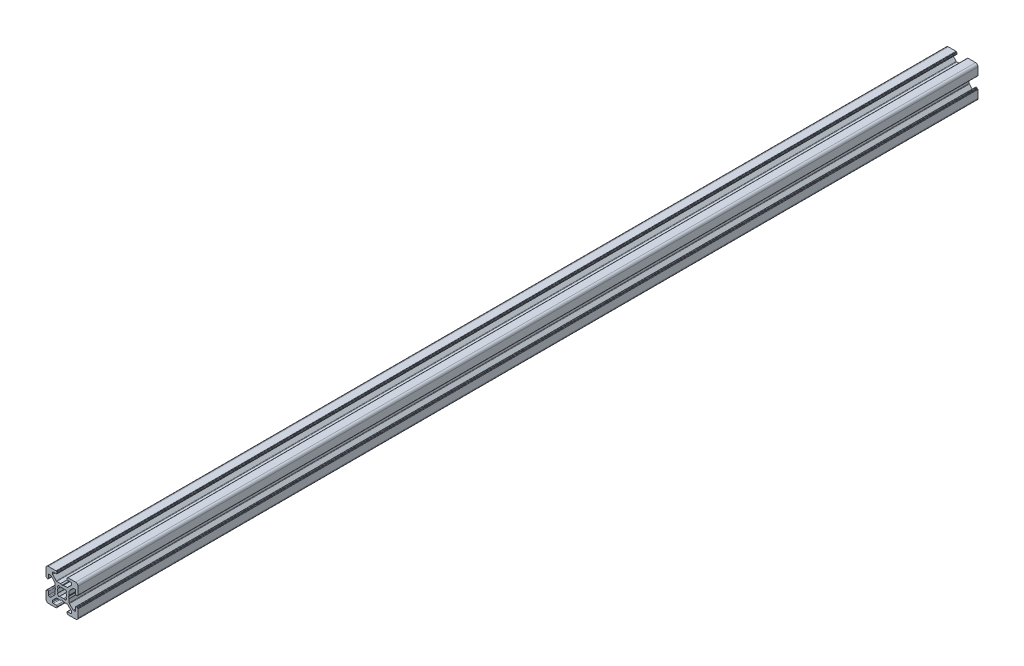
SolidWorks part; units mm, degrees
ref_plane "Front Plane" through (0, 0, 0) normal (0, 0, 1) x (1, 0, 0)
ref_plane "Top Plane" through (0, 0, 0) normal (0, 1, 0) x (1, 0, 0)
ref_plane "Right Plane" through (0, 0, 0) normal (1, 0, 0) x (0, 0, -1)
sketch "Sketch1" plane through (0, 0, 0) normal (0, 0, 1) x (1, 0, 0)
  line L0 (0, 13.3675) -> (0, -10.9159) construction
  line L1 (-12.9725, 0) -> (15.1887, 0) construction
  line L2 (-3.5, 8.5) -> (-5.5, 8.5)
  line L3 (-3.55, 9.7) -> (-3.55, 9.8)
  line L4 (-6, 7.2678) -> (-6, 8)
  line L5 (-7.2678, 6) -> (-8, 6)
  line L6 (-3.75, 10) -> (-8.5, 10)
  line L7 (-9.7, 3.55) -> (-9.8, 3.55)
  line L8 (-9.5, 3.2) -> (-9.5, 3.35)
  line L9 (-9, 3) -> (-9.3, 3)
  line L10 (-4.4732, 0.8536) -> (-4.0381, 0.1)
  line L11 (-4.5, 3.2322) -> (-4.5, 0.9536)
  line L12 (-8.5, 3.5) -> (-8.5, 5.5)
  line L13 (-10, 3.75) -> (-10, 8.5)
  line L14 (-3.5858, 4.6464) -> (-5.8536, 6.9142)
  line L15 (-4.6464, 3.5858) -> (-6.9142, 5.8536)
  line L16 (-3.2, 9.5) -> (-3.35, 9.5)
  line L17 (-3, 9) -> (-3, 9.3)
  line L18 (-0.8536, 4.4732) -> (-0.1, 4.0381)
  line L19 (-3.2322, 4.5) -> (-0.9536, 4.5)
  line L20 (-1.2582, 2.4453) -> (-1.9139, 2.9896)
  line L21 (-2.4453, 1.2582) -> (-2.9922, 1.9099)
  line L22 (3.5, -8.5) -> (5.5, -8.5)
  line L23 (3.55, -9.7) -> (3.55, -9.8)
  line L24 (6, -7.2678) -> (6, -8)
  line L25 (7.2678, -6) -> (8, -6)
  line L26 (3.75, -10) -> (8.5, -10)
  line L27 (9.7, -3.55) -> (9.8, -3.55)
  line L28 (9.5, -3.2) -> (9.5, -3.35)
  line L29 (9, -3) -> (9.3, -3)
  line L30 (4.4732, -0.8536) -> (4.0381, -0.1)
  line L31 (4.5, -3.2322) -> (4.5, -0.9536)
  line L32 (8.5, -3.5) -> (8.5, -5.5)
  line L33 (10, -3.75) -> (10, -8.5)
  line L34 (3.5858, -4.6464) -> (5.8536, -6.9142)
  line L35 (4.6464, -3.5858) -> (6.9142, -5.8536)
  line L36 (3.2, -9.5) -> (3.35, -9.5)
  line L37 (3, -9) -> (3, -9.3)
  line L38 (0.8536, -4.4732) -> (0.1, -4.0381)
  line L39 (3.2322, -4.5) -> (0.9536, -4.5)
  line L40 (1.2582, -2.4453) -> (1.9139, -2.9896)
  line L41 (2.4453, -1.2582) -> (2.9922, -1.9099)
  line L42 (-2.4453, -1.2582) -> (-2.9922, -1.9099)
  line L43 (-1.2582, -2.4453) -> (-1.9139, -2.9896)
  line L44 (-3.2322, -4.5) -> (-0.9536, -4.5)
  line L45 (-0.8536, -4.4732) -> (-0.1, -4.0381)
  line L46 (-3, -9) -> (-3, -9.3)
  line L47 (-3.2, -9.5) -> (-3.35, -9.5)
  line L48 (-4.6464, -3.5858) -> (-6.9142, -5.8536)
  line L49 (-3.5858, -4.6464) -> (-5.8536, -6.9142)
  line L50 (-10, -3.75) -> (-10, -8.5)
  line L51 (-8.5, -3.5) -> (-8.5, -5.5)
  line L52 (-4.5, -3.2322) -> (-4.5, -0.9536)
  line L53 (-4.4732, -0.8536) -> (-4.0381, -0.1)
  line L54 (-9, -3) -> (-9.3, -3)
  line L55 (-9.5, -3.2) -> (-9.5, -3.35)
  line L56 (-9.7, -3.55) -> (-9.8, -3.55)
  line L57 (2.4453, 1.2582) -> (2.9922, 1.9099)
  line L58 (1.2582, 2.4453) -> (1.9139, 2.9896)
  line L59 (3.2322, 4.5) -> (0.9536, 4.5)
  line L60 (0.8536, 4.4732) -> (0.1, 4.0381)
  line L61 (-3.75, -10) -> (-8.5, -10)
  line L62 (-7.2678, -6) -> (-8, -6)
  line L63 (-6, -7.2678) -> (-6, -8)
  line L64 (3, 9) -> (3, 9.3)
  line L65 (3.2, 9.5) -> (3.35, 9.5)
  line L66 (4.6464, 3.5858) -> (6.9142, 5.8536)
  line L67 (3.5858, 4.6464) -> (5.8536, 6.9142)
  line L68 (10, 3.75) -> (10, 8.5)
  line L69 (8.5, 3.5) -> (8.5, 5.5)
  line L70 (4.5, 3.2322) -> (4.5, 0.9536)
  line L71 (4.4732, 0.8536) -> (4.0381, 0.1)
  line L72 (9, 3) -> (9.3, 3)
  line L73 (9.5, 3.2) -> (9.5, 3.35)
  line L74 (9.7, 3.55) -> (9.8, 3.55)
  line L75 (3.75, 10) -> (8.5, 10)
  line L76 (7.2678, 6) -> (8, 6)
  line L77 (6, 7.2678) -> (6, 8)
  line L78 (3.55, 9.7) -> (3.55, 9.8)
  line L79 (3.5, 8.5) -> (5.5, 8.5)
  line L80 (-3.55, -9.7) -> (-3.55, -9.8)
  line L81 (-3.5, -8.5) -> (-5.5, -8.5)
  arc A0 (-10, 8.5) -> (-8.5, 10) centre (-8.5, 8.5) cw
  arc A1 (-8.5, 5.5) -> (-8, 6) centre (-8, 5.5) cw
  arc A2 (-7.2678, 6) -> (-6.9142, 5.8536) centre (-7.2678, 5.5) cw
  arc A3 (-5.8536, 6.9142) -> (-6, 7.2678) centre (-5.5, 7.2678) cw
  arc A4 (-6, 8) -> (-5.5, 8.5) centre (-5.5, 8) cw
  arc A5 (-9.7, 3.55) -> (-9.5, 3.35) centre (-9.7, 3.35) cw
  arc A6 (-9.8, 3.55) -> (-10, 3.75) centre (-9.8, 3.75) cw
  arc A7 (-9.3, 3) -> (-9.5, 3.2) centre (-9.3, 3.2) cw
  arc A8 (-8.5, 3.5) -> (-9, 3) centre (-9, 3.5) cw
  arc A9 (-4.6464, 3.5858) -> (-4.5, 3.2322) centre (-5, 3.2322) cw
  arc A10 (-4.4732, 0.8536) -> (-4.5, 0.9536) centre (-4.3, 0.9536) cw
  arc A11 (-4.0381, 0.1) -> (-4.0381, -0.1) centre (-4.2113, 0) cw
  arc A12 (-3.2, 9.5) -> (-3, 9.3) centre (-3.2, 9.3) cw
  arc A13 (-0.9536, 4.5) -> (-0.8536, 4.4732) centre (-0.9536, 4.3) cw
  arc A14 (-2.9922, 1.9099) -> (-1.9139, 2.9896) centre (0, 0) cw
  arc A15 (-3.2322, 4.5) -> (-3.5858, 4.6464) centre (-3.2322, 5) cw
  arc A16 (-3.75, 10) -> (-3.55, 9.8) centre (-3.75, 9.8) cw
  arc A17 (-3.35, 9.5) -> (-3.55, 9.7) centre (-3.35, 9.7) cw
  arc A18 (2.4453, -1.2582) -> (2.4453, 1.2582) centre (0, 0) ccw
  arc A19 (-3, 9) -> (-3.5, 8.5) centre (-3.5, 9) cw
  arc A20 (-2.4453, -1.2582) -> (-2.4453, 1.2582) centre (0, 0) cw
  arc A21 (10, -8.5) -> (8.5, -10) centre (8.5, -8.5) cw
  arc A22 (8.5, -5.5) -> (8, -6) centre (8, -5.5) cw
  arc A23 (7.2678, -6) -> (6.9142, -5.8536) centre (7.2678, -5.5) cw
  arc A24 (5.8536, -6.9142) -> (6, -7.2678) centre (5.5, -7.2678) cw
  arc A25 (6, -8) -> (5.5, -8.5) centre (5.5, -8) cw
  arc A26 (9.7, -3.55) -> (9.5, -3.35) centre (9.7, -3.35) cw
  arc A27 (9.8, -3.55) -> (10, -3.75) centre (9.8, -3.75) cw
  arc A28 (9.3, -3) -> (9.5, -3.2) centre (9.3, -3.2) cw
  arc A29 (8.5, -3.5) -> (9, -3) centre (9, -3.5) cw
  arc A30 (4.6464, -3.5858) -> (4.5, -3.2322) centre (5, -3.2322) cw
  arc A31 (4.4732, -0.8536) -> (4.5, -0.9536) centre (4.3, -0.9536) cw
  arc A32 (3.2, -9.5) -> (3, -9.3) centre (3.2, -9.3) cw
  arc A33 (-0.1, -4.0381) -> (0.1, -4.0381) centre (0, -4.2113) cw
  arc A34 (0.9536, -4.5) -> (0.8536, -4.4732) centre (0.9536, -4.3) cw
  arc A35 (2.9922, -1.9099) -> (1.9139, -2.9896) centre (0, 0) cw
  arc A36 (1.2582, -2.4453) -> (-1.2582, -2.4453) centre (0, 0) cw
  arc A37 (3.2322, -4.5) -> (3.5858, -4.6464) centre (3.2322, -5) cw
  arc A38 (3.75, -10) -> (3.55, -9.8) centre (3.75, -9.8) cw
  arc A39 (3.35, -9.5) -> (3.55, -9.7) centre (3.35, -9.7) cw
  arc A40 (3, -9) -> (3.5, -8.5) centre (3.5, -9) cw
  arc A41 (-3, -9) -> (-3.5, -8.5) centre (-3.5, -9) ccw
  arc A42 (-3.35, -9.5) -> (-3.55, -9.7) centre (-3.35, -9.7) ccw
  arc A43 (-3.75, -10) -> (-3.55, -9.8) centre (-3.75, -9.8) ccw
  arc A44 (-3.2322, -4.5) -> (-3.5858, -4.6464) centre (-3.2322, -5) ccw
  arc A45 (-2.9922, -1.9099) -> (-1.9139, -2.9896) centre (0, 0) ccw
  arc A46 (-0.9536, -4.5) -> (-0.8536, -4.4732) centre (-0.9536, -4.3) ccw
  arc A47 (-3.2, -9.5) -> (-3, -9.3) centre (-3.2, -9.3) ccw
  arc A48 (-4.4732, -0.8536) -> (-4.5, -0.9536) centre (-4.3, -0.9536) ccw
  arc A49 (3, 9) -> (3.5, 8.5) centre (3.5, 9) ccw
  arc A50 (3.35, 9.5) -> (3.55, 9.7) centre (3.35, 9.7) ccw
  arc A51 (3.75, 10) -> (3.55, 9.8) centre (3.75, 9.8) ccw
  arc A52 (3.2322, 4.5) -> (3.5858, 4.6464) centre (3.2322, 5) ccw
  arc A53 (1.2582, 2.4453) -> (-1.2582, 2.4453) centre (0, 0) ccw
  arc A54 (-4.6464, -3.5858) -> (-4.5, -3.2322) centre (-5, -3.2322) ccw
  arc A55 (-8.5, -3.5) -> (-9, -3) centre (-9, -3.5) ccw
  arc A56 (-9.3, -3) -> (-9.5, -3.2) centre (-9.3, -3.2) ccw
  arc A57 (-9.8, -3.55) -> (-10, -3.75) centre (-9.8, -3.75) ccw
  arc A58 (-9.7, -3.55) -> (-9.5, -3.35) centre (-9.7, -3.35) ccw
  arc A59 (-6, -8) -> (-5.5, -8.5) centre (-5.5, -8) ccw
  arc A60 (2.9922, 1.9099) -> (1.9139, 2.9896) centre (0, 0) ccw
  arc A61 (0.9536, 4.5) -> (0.8536, 4.4732) centre (0.9536, 4.3) ccw
  arc A62 (-0.1, 4.0381) -> (0.1, 4.0381) centre (0, 4.2113) ccw
  arc A63 (-5.8536, -6.9142) -> (-6, -7.2678) centre (-5.5, -7.2678) ccw
  arc A64 (-7.2678, -6) -> (-6.9142, -5.8536) centre (-7.2678, -5.5) ccw
  arc A65 (-8.5, -5.5) -> (-8, -6) centre (-8, -5.5) ccw
  arc A66 (-10, -8.5) -> (-8.5, -10) centre (-8.5, -8.5) ccw
  arc A67 (3.2, 9.5) -> (3, 9.3) centre (3.2, 9.3) ccw
  arc A68 (4.0381, 0.1) -> (4.0381, -0.1) centre (4.2113, 0) ccw
  arc A69 (4.4732, 0.8536) -> (4.5, 0.9536) centre (4.3, 0.9536) ccw
  arc A70 (4.6464, 3.5858) -> (4.5, 3.2322) centre (5, 3.2322) ccw
  arc A71 (8.5, 3.5) -> (9, 3) centre (9, 3.5) ccw
  arc A72 (9.3, 3) -> (9.5, 3.2) centre (9.3, 3.2) ccw
  arc A73 (9.8, 3.55) -> (10, 3.75) centre (9.8, 3.75) ccw
  arc A74 (9.7, 3.55) -> (9.5, 3.35) centre (9.7, 3.35) ccw
  arc A75 (6, 8) -> (5.5, 8.5) centre (5.5, 8) ccw
  arc A76 (5.8536, 6.9142) -> (6, 7.2678) centre (5.5, 7.2678) ccw
  arc A77 (7.2678, 6) -> (6.9142, 5.8536) centre (7.2678, 5.5) ccw
  arc A78 (8.5, 5.5) -> (8, 6) centre (8, 5.5) ccw
  arc A79 (10, 8.5) -> (8.5, 10) centre (8.5, 8.5) ccw
  dimension "D4" = 5.5
  dimension "D1" = 6
  dimension "D2" = 20
  dimension "D3" = 20
  dimension "D5" = 5.5
  dimension "D6" = 10
  dimension "D7" = 6
  dimension "D8" = 6
  dimension "D9" = 6
extrude "Extrude1" add sketch "Sketch1" along normal blind 561.63
